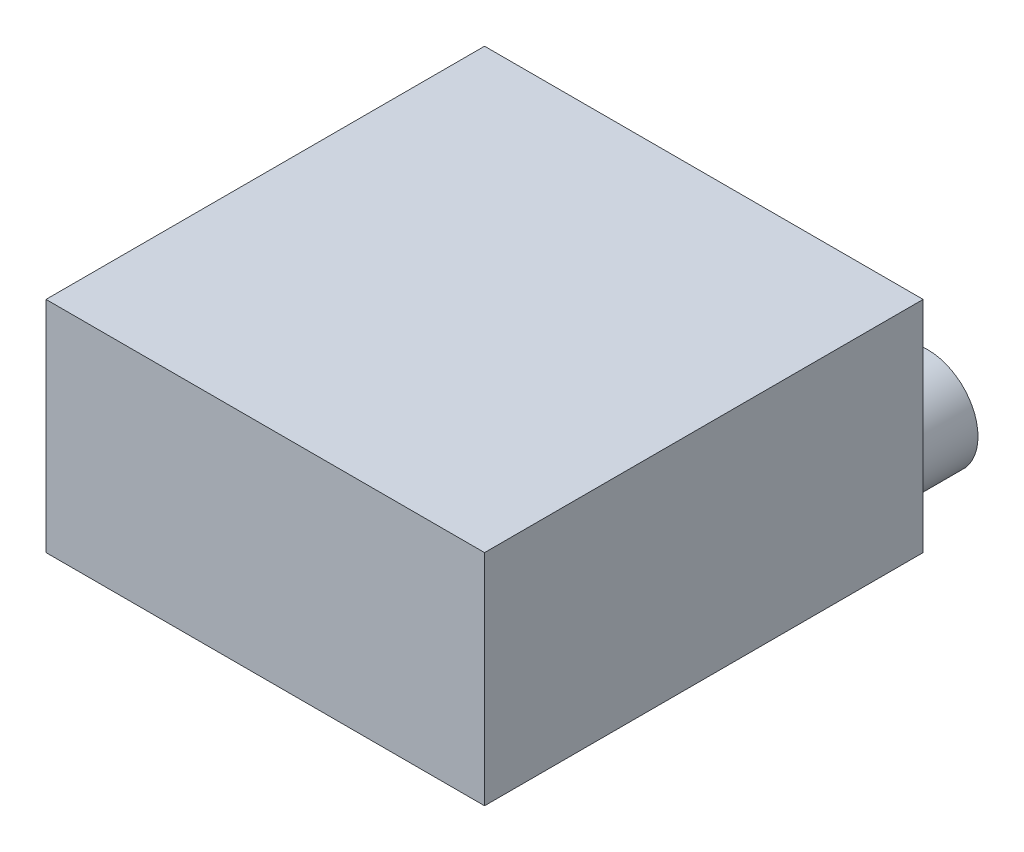
SolidWorks part; units mm, degrees
ref_plane "Front Plane" through (0, 0, 0) normal (0, 0, 1) x (1, 0, 0)
ref_plane "Top Plane" through (0, 0, 0) normal (0, 1, 0) x (1, 0, 0)
ref_plane "Right Plane" through (0, 0, 0) normal (1, 0, 0) x (0, 0, -1)
sketch "Sketch1" plane through (0, 0, 0) normal (0, 1, 0) x (1, 0, 0)
  line L1 (-4.6985, 0.6533) -> (5.3015, 0.6533)
  line L2 (-4.6985, 0.6533) -> (-4.6985, -9.3467)
  line L3 (-4.6985, -9.3467) -> (5.3015, -9.3467)
  line L4 (5.3015, 0.6533) -> (5.3015, -9.3467)
  dimension "D1" = 10
  dimension "D2" = 10
extrude "Boss-Extrude1" add sketch "Sketch1" along normal blind 5
sketch "Sketch2" plane through (0, 0, -0.6533) normal (0, 0, -1) x (-1, 0, 0)
  circle A0 centre (-3.9094, 1.4164) radius 1.1434
extrude "Boss-Extrude2" add sketch "Sketch2" along normal blind 1.5
